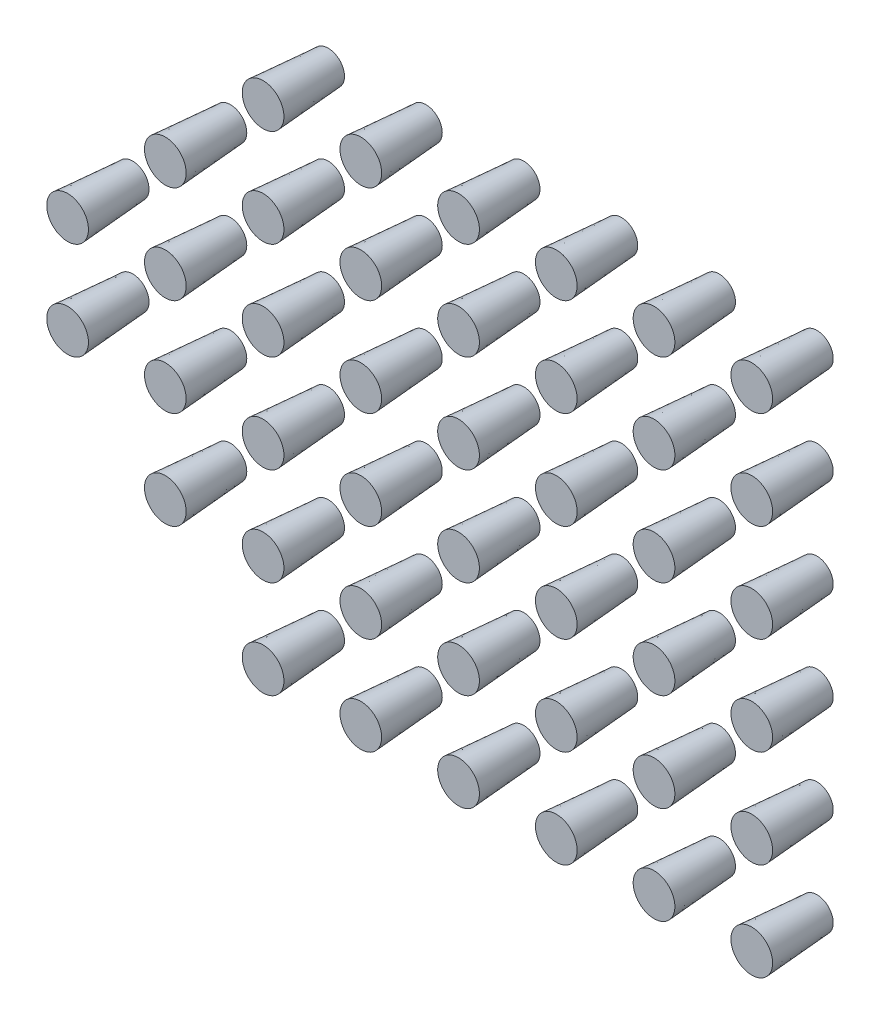
SolidWorks part; units mm, degrees
ref_plane "前视基准面" through (0, 0, 0) normal (0, 0, 1) x (1, 0, 0)
ref_plane "上视基准面" through (0, 0, 0) normal (0, 1, 0) x (1, 0, 0)
ref_plane "右视基准面" through (0, 0, 0) normal (1, 0, 0) x (0, 0, -1)
other "Configuration Table"
sketch "草图1" plane through (0, 0, 0) normal (0, 0, 1) x (1, 0, 0)
  circle A0 centre (0, 0) radius 0.5
  dimension "D1" = 1
extrude "凸台-拉伸1" add sketch "草图1" along normal blind 2 draft 4 draft outward yes
pattern_linear "阵列(线性)1" count 6 spacing 3 along (0, 1, 0) count 6 spacing 3 along (1, 0, 0) of "凸台-拉伸1"
ref_plane "基准面1" through (7.5, 0, 0) normal (1, 0, 0) x (0, 0, -1)
ref_plane "基准面2" through (0, 7.5, 0) normal (0, 1, 0) x (1, 0, 0)
pattern_linear "阵列(线性)2" count 2 spacing 3 along (-1, 0, 0) of bodies 110 109 108 107
pattern_linear "阵列(线性)3" count 2 spacing 3 along (-1, 0, 0) of bodies 143 144
